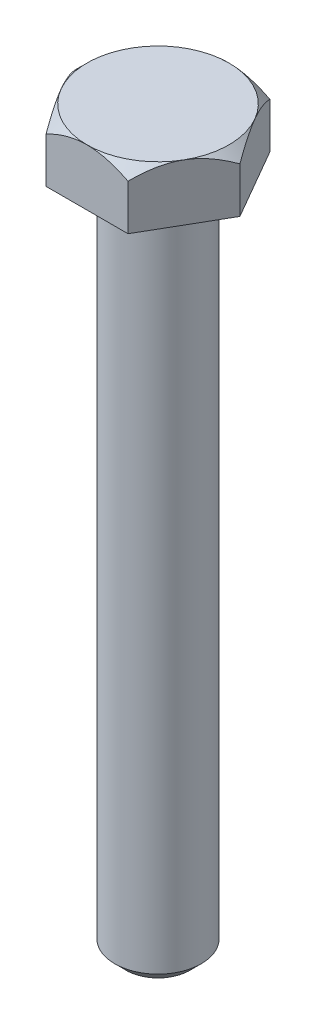
SolidWorks part; units mm, degrees
ref_plane "Спереди" through (0, 0, 0) normal (0, 0, 1) x (1, 0, 0)
ref_plane "Сверху" through (0, 0, 0) normal (0, 1, 0) x (1, 0, 0)
ref_plane "Справа" through (0, 0, 0) normal (1, 0, 0) x (0, 0, -1)
sketch "Эскиз6" plane through (0, 0, 0) normal (0, 1, 0) x (1, 0, 0)
  line L1 (7.25, 0) -> (3.625, 6.2787)
  line L2 (3.625, 6.2787) -> (-3.625, 6.2787)
  line L3 (-3.625, 6.2787) -> (-7.25, 0)
  line L4 (-7.25, 0) -> (-3.625, -6.2787)
  line L5 (-3.625, -6.2787) -> (3.625, -6.2787)
  line L6 (3.625, -6.2787) -> (7.25, 0)
  circle A0 centre (0, 0) radius 6.2787 construction
  dimension "D1" = 14.5
extrude "Бобышка-Вытянуть1" add sketch "Эскиз6" along normal blind 5
sketch "Эскиз8" plane through (0, 5, 0) normal (0, 1, 0) x (1, 0, 0)
  circle A0 centre (0, 0) radius 6.2787
extrude "Вырез-Вытянуть1" cut sketch "Эскиз8" against normal blind 1 draft 45 flip side to cut
sketch "Эскиз9" plane through (0, 0, 0) normal (0, -1, 0) x (1, 0, 0)
  circle A0 centre (0, 0) radius 3.825
  dimension "D1" = 7.65
extrude "bolt length" add sketch "Эскиз9" along normal blind 60
fillet "Скругление1" radius 1 1 edges at (0, 0, 3.825)
chamfer "Фаска1" distance 1 angle 45 1 edges at (0, -60, -3.825)
